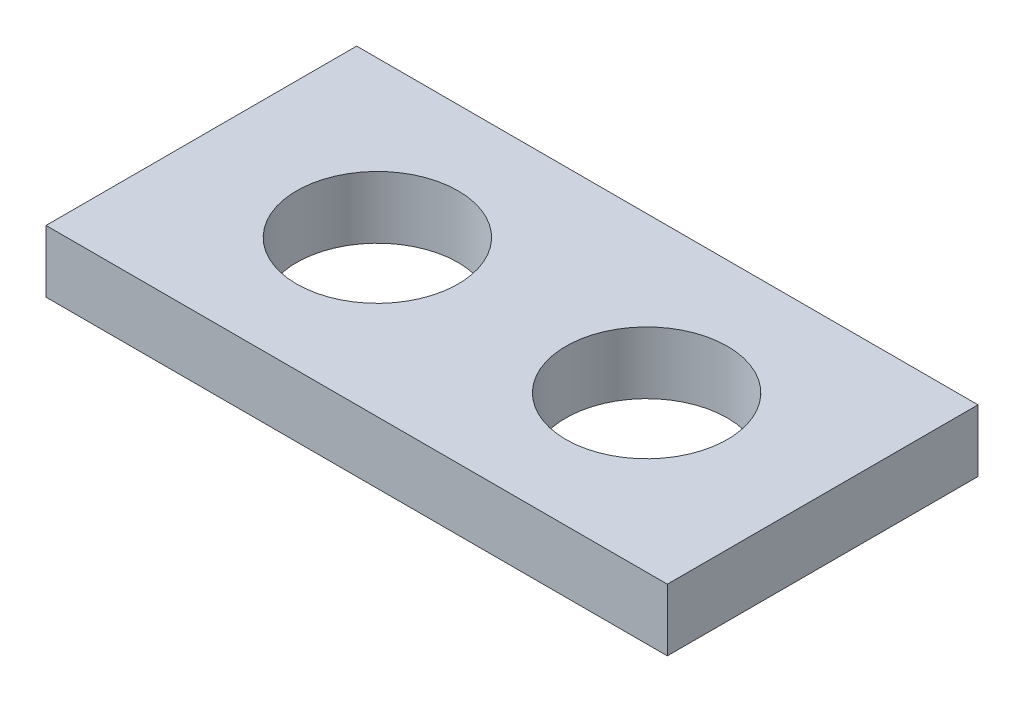
SolidWorks part; units mm, degrees
ref_plane "Front Plane" through (0, 0, 0) normal (0, 0, 1) x (1, 0, 0)
ref_plane "Top Plane" through (0, 0, 0) normal (0, 1, 0) x (1, 0, 0)
ref_plane "Right Plane" through (0, 0, 0) normal (1, 0, 0) x (0, 0, -1)
sketch "Sketch1" plane through (0, 0, 0) normal (0, 1, 0) x (1, 0, 0)
  line L1 (-15, -7.5) -> (15, -7.5)
  line L2 (-15, -7.5) -> (-15, 7.5)
  line L3 (-15, 7.5) -> (15, 7.5)
  line L4 (15, -7.5) -> (15, 7.5)
  line L5 (-15, -7.5) -> (15, 7.5) construction
  line L6 (-15, 7.5) -> (15, -7.5) construction
  point P0 (0, 0)
  dimension "D1" = 30
  dimension "D2" = 15
extrude "Boss-Extrude1" add sketch "Sketch1" along normal blind 3
sketch "Sketch2" plane through (0, 3, 0) normal (0, 1, 0) x (1, 0, 0)
  circle A0 centre (-6.5, 0) radius 3.9
  dimension "D2" = 7.8
  dimension "D1" = 6.5
extrude "Cut-Extrude1" cut sketch "Sketch2" against normal through all both and the other way through all
mirror "Mirror1" about plane through (0, 0, 0) normal (1, 0, 0) of "Cut-Extrude1"
